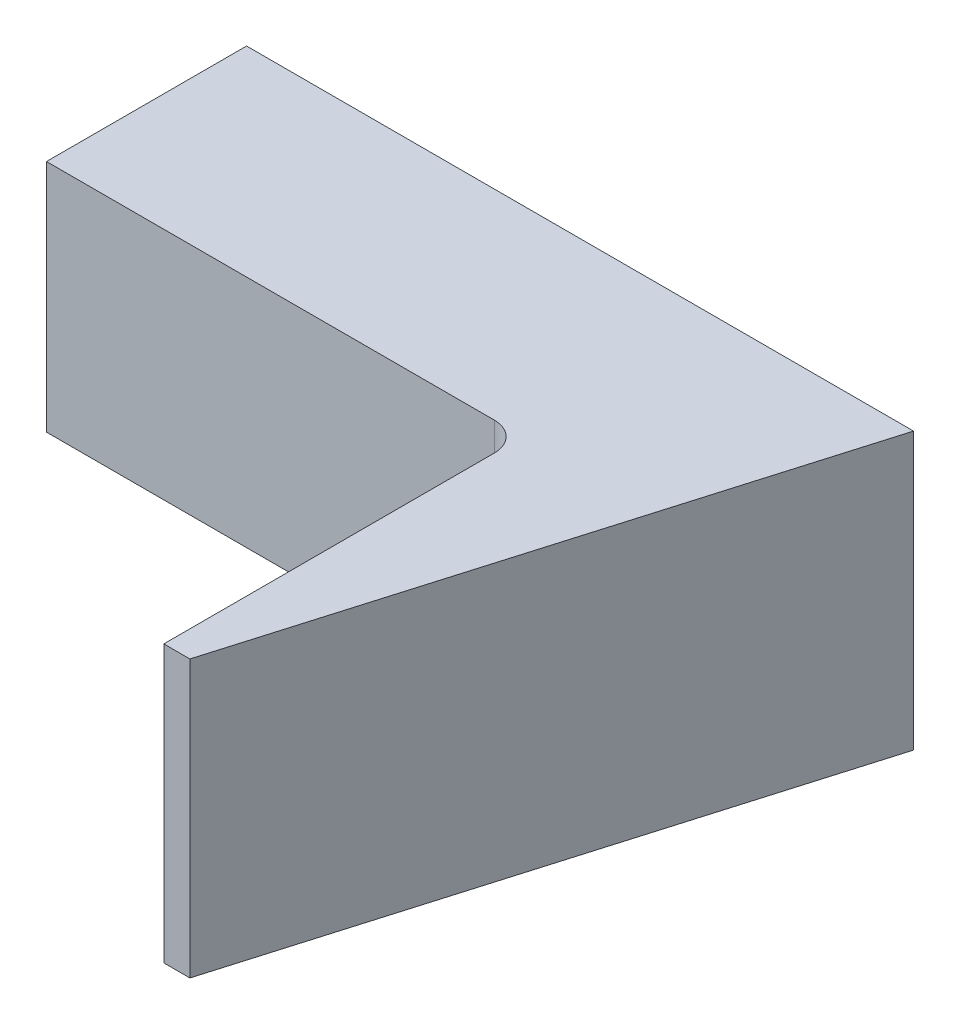
SolidWorks part; units mm, degrees
other "Markup1"
sketch "Sketch31"
material "Zinc AG40A (Zn-4Al-0.4Mg; Zamak 3), Cast"
ref_plane "Front Plane" through (0, 0, 0) normal (0, 0, 1) x (1, 0, 0)
ref_plane "Top Plane" through (0, 0, 0) normal (0, 1, 0) x (1, 0, 0)
ref_plane "Right Plane" through (0, 0, 0) normal (1, 0, 0) x (0, 0, -1)
sketch "Sketch2" plane through (0, 0, 0) normal (0, 0, 1) x (1, 0, 0)
  line L0 (-5.08, 0) -> (-5.08, -1.524)
  line L1 (-25.4, 9.398) -> (0, 9.398)
  line L2 (-5.08, -1.524) -> (0, -1.524)
  line L3 (0, 0) -> (0, -1.524)
  line L4 (-25.4, 9.398) -> (-25.4, 0)
  line L11 (-25.4, 0) -> (-5.08, 0)
  line L15 (0, 9.398) -> (0, 0)
  dimension "D2" = 1.524
  dimension "D3" = 5.08
  dimension "D7" = 9.398
  dimension "D15" = 25.4
extrude "Extrude1" add sketch "Sketch2" along normal blind 5.334
sketch "Sketch20" plane through (0, 0, 5.334) normal (0, 0, 1) x (1, 0, 0)
  line L0 (0, 9.398) -> (-25.4, 9.398) construction
  line L1 (0, 9.398) -> (-5.08, 9.398)
  line L2 (0, 9.398) -> (0, 3.683)
  line L3 (0, 3.683) -> (-5.08, 3.683)
  line L4 (-5.08, 9.398) -> (-5.08, 3.683)
  line L5 (0, -1.524) -> (0, 9.398) construction
  dimension "D1" = 5.08
  dimension "D2" = 0
  dimension "D3" = 5.715
extrude "Extrude3" add sketch "Sketch20" along normal blind 12.7
sketch "Sketch22" plane through (0, 0, 5.334) normal (0, 0, 1) x (1, 0, 0)
  line L0 (-25.4, 9.398) -> (-26.289, 9.398)
  line L1 (-26.289, 9.398) -> (-26.289, 6.858)
  line L2 (-26.289, 6.858) -> (-25.4, 6.858)
  line L3 (-25.4, 9.398) -> (-25.4, 0) construction
  line L4 (-25.4, 9.398) -> (-25.4, 6.858)
  dimension "D2" = 2.54
  dimension "D1" = 0.889
extrude "Extrude5" add sketch "Sketch22" against normal up to surface (5.334 mm away) up to face at (-10.16, 2.6247, 0)
sketch "Sketch23" plane through (0, 3.683, 0) normal (0, -1, 0) x (1, 0, 0)
  line L0 (-5.08, 18.034) -> (-5.08, 5.334) construction
  line L1 (0, 18.034) -> (0, 5.334) construction
  line L2 (-5.08, 18.034) -> (0, 18.034) construction
  line L3 (-5.08, 18.034) -> (-5.08, 16.4465)
  line L4 (0, 18.034) -> (0, 16.4465)
  line L5 (-5.08, 18.034) -> (0, 18.034)
  line L6 (-5.08, 16.4465) -> (0, 16.4465)
  dimension "D1" = 1.5875
extrude "Extrude6" add sketch "Sketch23" along normal up to surface (3.683 mm away) up to face at (-15.24, 0, 2.667)
fillet "Fillet5" radius 1.6002 1 edges at (-26.289, 8.128, 5.334)
fillet "Fillet6" radius 0.8382 1 edges at (-5.08, 1.8415, 16.4465)
fillet "Fillet2" radius 0.762 8 edges at (0, 4.699, 18.034) (-5.08, 4.699, 18.034) (-5.08, 0, 17.6593) (-5.08, 1.8415, 17.2847)
sketch "Sketch26" plane through (0, 9.398, 0) normal (0, 1, 0) x (1, 0, 0)
  line L0 (0, 0) -> (-5.08, -17.272)
  arc A0 (-5.08, -17.272) -> (-4.318, -18.034) centre (-4.318, -17.272) ccw construction
extrude "Cut-Extrude4" cut sketch "Sketch26" against normal through all and the other way through all
sketch "Sketch27" plane through (0, 9.398, 0) normal (0, 1, 0) x (1, 0, 0)
  line L0 (-5.08, -14.9068) -> (-4.3843, -14.9068)
  line L1 (-5.08, -17.272) -> (-5.08, -6.096) construction
  line L2 (0, 0) -> (-5.08, -17.272) construction
extrude "Cut-Extrude5" cut sketch "Sketch27" against normal through all and the other way through all flip side to cut
sketch "Sketch28" plane through (0, 9.398, 0) normal (0, 1, 0) x (1, 0, 0)
  line L0 (-17.78, 0) -> (-17.78, -5.334)
  line L1 (0, 0) -> (-26.289, 0) construction
  line L2 (-5.842, -5.334) -> (-24.6888, -5.334) construction
  line L3 (-5.08, -14.9068) -> (-5.08, -6.096) construction
  point P8 (-5.08, -10.5014)
  dimension "D1" = 12.7
extrude "Cut-Extrude7" cut sketch "Sketch28" against normal through all and the other way through all flip side to cut
sketch "Sketch29" plane through (-17.78, 0, 0) normal (-1, 0, 0) x (0, 0, 1)
  line L0 (0, 3.1496) -> (5.334, 3.1496)
  line L1 (0, 9.398) -> (0, 0) construction
  line L2 (5.334, 9.398) -> (5.334, 0) construction
  line L3 (0, 9.398) -> (5.334, 9.398) construction
  dimension "D1" = 6.2484
extrude "Cut-Extrude8" cut sketch "Sketch29" against normal through all and the other way through all flip side to cut
sketch "Sketch30" plane through (0, 9.398, 0) normal (0, 1, 0) x (1, 0, 0)
  line L0 (-5.08, -14.9068) -> (-5.08, 0)
  line L1 (0, 0) -> (-17.78, 0) construction
  line L2 (-5.08, 0) -> (0, 0)
  line L3 (0, 0) -> (-4.3843, -14.9068)
  line L4 (-4.3843, -14.9068) -> (-5.08, -14.9068)
extrude "Boss-Extrude1" add sketch "Sketch30" against normal blind 7.366
